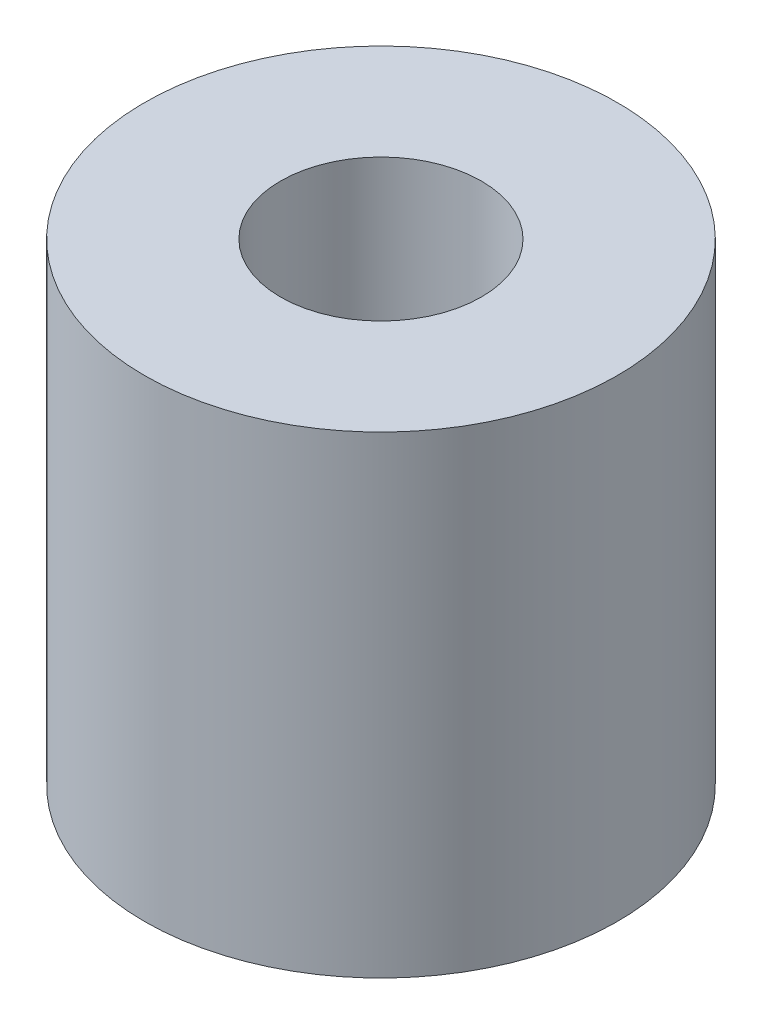
SolidWorks part; units mm, degrees
ref_plane "Front Plane" through (0, 0, 0) normal (0, 0, 1) x (1, 0, 0)
ref_plane "Top Plane" through (0, 0, 0) normal (0, 1, 0) x (1, 0, 0)
ref_plane "Right Plane" through (0, 0, 0) normal (1, 0, 0) x (0, 0, -1)
sketch "Sketch1" plane through (0, 0, 0) normal (0, 1, 0) x (1, 0, 0)
  circle A0 centre (0, 0) radius 2.125
  circle A1 centre (0, 0) radius 5
  dimension "D1" = 4.25
  dimension "D2" = 10
extrude "Boss-Extrude1" add sketch "Sketch1" along normal blind 10
